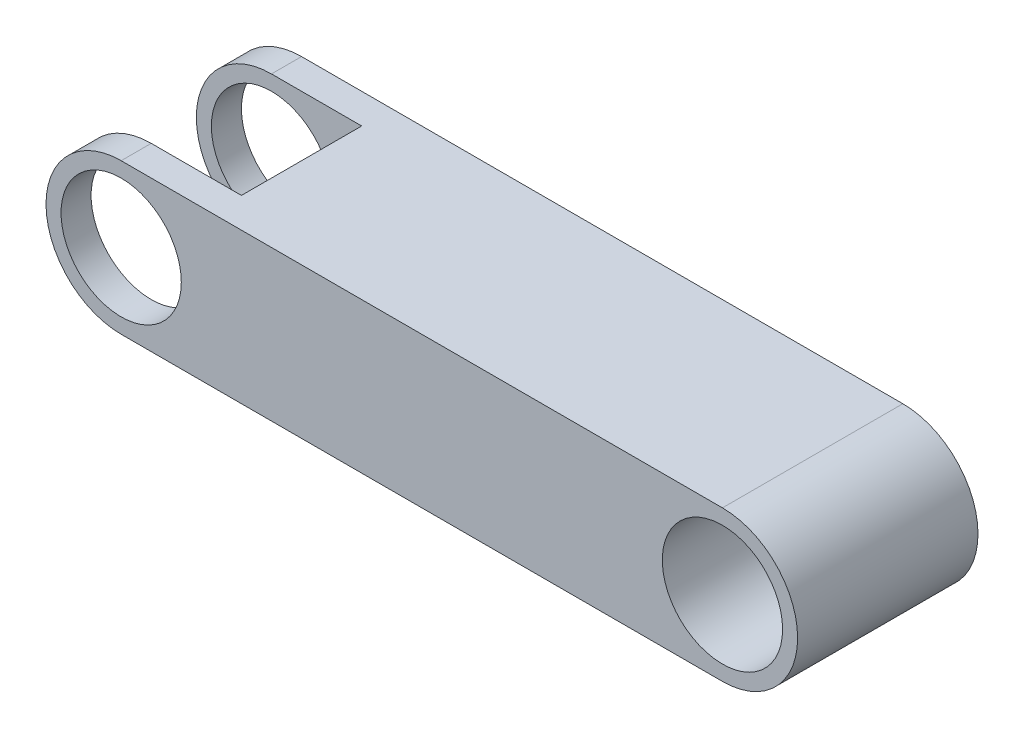
SolidWorks part; units mm, degrees
ref_plane "Front Plane" through (0, 0, 0) normal (0, 0, 1) x (1, 0, 0)
ref_plane "Top Plane" through (0, 0, 0) normal (0, 1, 0) x (1, 0, 0)
ref_plane "Right Plane" through (0, 0, 0) normal (1, 0, 0) x (0, 0, -1)
sketch "Sketch3" plane through (0, 0, 0) normal (0, 0, 1) x (1, 0, 0)
  line L0 (0, 0) -> (100, 0) construction
  line L1 (0, 12.5) -> (100, 12.5)
  line L2 (0, -12.5) -> (100, -12.5)
  arc A0 (0, 12.5) -> (0, -12.5) centre (0, 0) ccw
  arc A1 (100, -12.5) -> (100, 12.5) centre (100, 0) ccw
  circle A2 centre (0, 0) radius 10
  circle A3 centre (100, 0) radius 10
  point P2 (50, 0)
  point P11 (0, 0)
  dimension "D1" = 20
  dimension "D2" = 25
  dimension "D3" = 100
extrude "Boss-Extrude2" add sketch "Sketch3" along normal mid plane 30
sketch "Sketch4" plane through (0, 0, 0) normal (1, 0, 0) x (0, 0, -1)
  line L0 (-15, 12.5) -> (15, 12.5) construction
  line L1 (-10, -12.5) -> (10, -12.5)
  line L2 (-10, -12.5) -> (-10, 12.5)
  line L3 (-10, 12.5) -> (10, 12.5)
  line L4 (10, -12.5) -> (10, 12.5)
  line L5 (-10, -12.5) -> (10, 12.5) construction
  line L6 (-10, 12.5) -> (10, -12.5) construction
  point P0 (0, 0)
  dimension "D1" = 20
extrude "Cut-Extrude2" cut sketch "Sketch4" against normal mid plane 30
